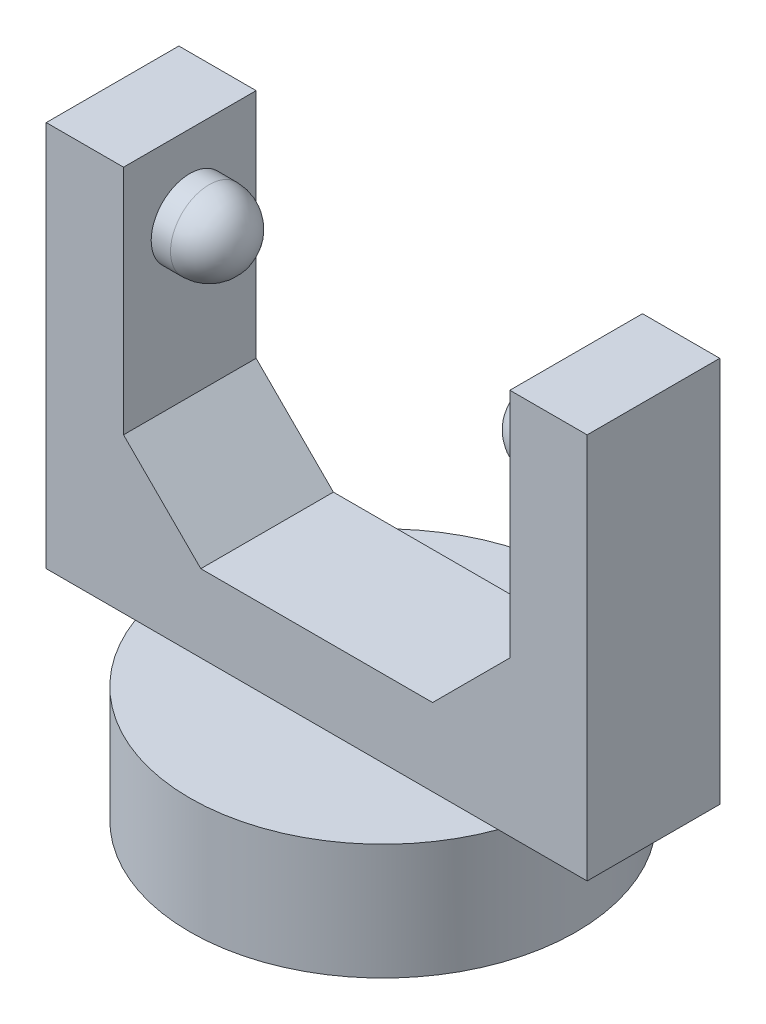
SolidWorks part; units mm, degrees
ref_plane "Front Plane" through (0, 0, 0) normal (0, 0, 1) x (1, 0, 0)
ref_plane "Top Plane" through (0, 0, 0) normal (0, 1, 0) x (1, 0, 0)
ref_plane "Right Plane" through (0, 0, 0) normal (1, 0, 0) x (0, 0, -1)
sketch "Sketch1" plane through (0, 0, 0) normal (0, 1, 0) x (1, 0, 0)
  circle A0 centre (0, 0) radius 12.5
  dimension "D1" = 25
extrude "Boss-Extrude1" add sketch "Sketch1" along normal blind 7.5
sketch "Sketch2" plane through (0, 7.5, 0) normal (0, 1, 0) x (1, 0, 0)
  line L1 (-17.5, 4.2904) -> (17.5, 4.2904)
  line L2 (-17.5, 4.2904) -> (-17.5, -4.2904)
  line L3 (-17.5, -4.2904) -> (17.5, -4.2904)
  line L4 (17.5, 4.2904) -> (17.5, -4.2904)
  point P4 (17.5, 0)
  point P6 (0, 4.2904)
  dimension "D1" = 35
  dimension "D3" = 8.5808
extrude "Boss-Extrude2" add sketch "Sketch2" along normal blind 25
sketch "Sketch3" plane through (0, 32.5, 0) normal (0, 1, 0) x (1, 0, 0)
  line L0 (17.5, 4.2904) -> (-17.5, 4.2904) construction
  line L1 (-12.5, 4.2904) -> (12.5, 4.2904)
  line L2 (-12.5, 4.2904) -> (-12.5, -4.2904)
  line L3 (-12.5, -4.2904) -> (12.5, -4.2904)
  line L4 (12.5, 4.2904) -> (12.5, -4.2904)
  line L5 (-17.5, -4.2904) -> (17.5, -4.2904) construction
  line L6 (17.5, -4.2904) -> (17.5, 4.2904) construction
  line L7 (-17.5, 4.2904) -> (-17.5, -4.2904) construction
  dimension "D1" = 5
  dimension "D2" = 5
extrude "Cut-Extrude1" cut sketch "Sketch3" against normal blind 20
sketch "Sketch4" plane through (-12.5, 0, 0) normal (1, 0, 0) x (0, 0, -1)
  line L0 (4.2904, 12.5) -> (-4.2904, 12.5) construction
  line L1 (4.2904, 32.5) -> (-4.2904, 32.5) construction
  circle A0 centre (0, 27.5) radius 2.5
  point P8 (0, 32.5)
  dimension "D1" = 5
  dimension "D2" = 15
extrude "Boss-Extrude3" add sketch "Sketch4" along normal blind 3.75
sketch "Sketch5" plane through (12.5, 0, 0) normal (-1, 0, 0) x (0, 0, 1)
  circle A0 centre (0, 27.5) radius 2.5
  circle A1 centre (0, 27.5) radius 2.5 construction
  dimension "D1" = 5
extrude "Boss-Extrude4" add sketch "Sketch5" along normal blind 3.75
fillet "Fillet2" radius 2.5 1 edges at (-8.75, 27.5, -2.5)
fillet "Fillet3" radius 2.5 1 edges at (8.75, 27.5, 2.5)
chamfer "Chamfer1" distance 5 angle 45 1 edges at (-12.5, 12.5, 0)
chamfer "Chamfer2" distance 5 angle 45 1 edges at (12.5, 12.5, 0)
